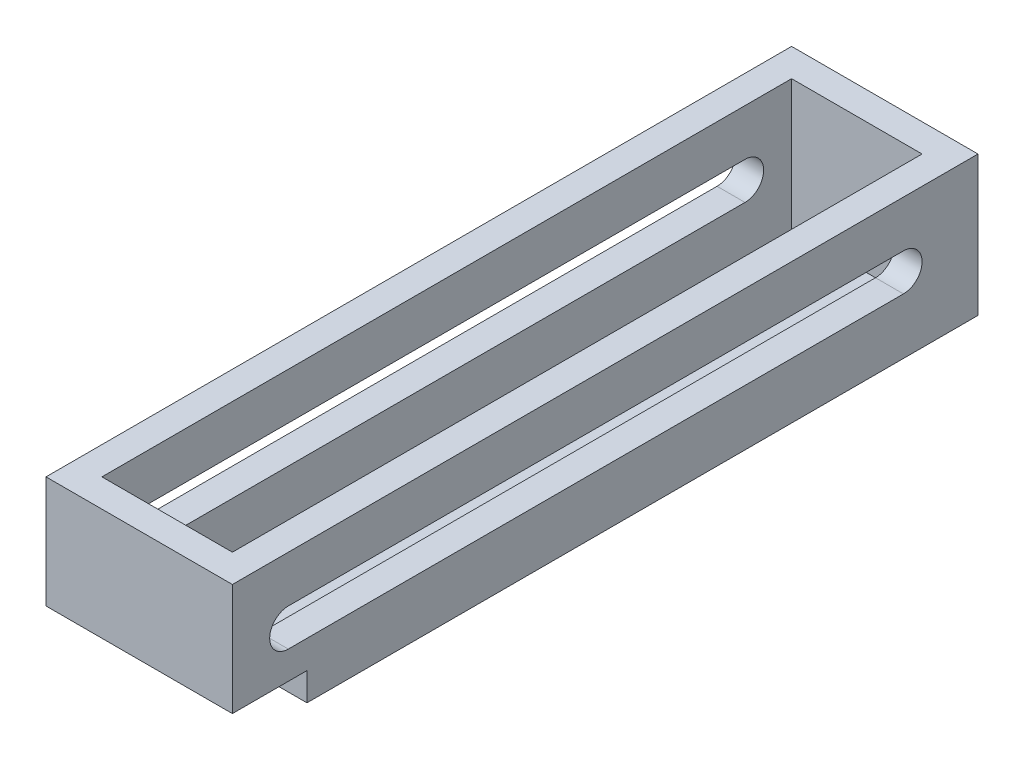
SolidWorks part; units mm, degrees
material "Oak"
ref_plane "Front Plane" through (0, 0, 0) normal (0, 0, 1) x (1, 0, 0)
ref_plane "Top Plane" through (0, 0, 0) normal (0, 1, 0) x (1, 0, 0)
ref_plane "Right Plane" through (0, 0, 0) normal (1, 0, 0) x (0, 0, -1)
other "Configuration Table"
sketch "Sketch1" plane through (0, 0, 0) normal (0, 1, 0) x (1, 0, 0)
  line L1 (-63.5, 254) -> (63.5, 254)
  line L2 (-63.5, 254) -> (-63.5, -254)
  line L3 (-63.5, -254) -> (63.5, -254)
  line L4 (63.5, 254) -> (63.5, -254)
  line L5 (-63.5, 254) -> (63.5, -254) construction
  line L6 (-63.5, -254) -> (63.5, 254) construction
  point P0 (0, 0)
  dimension "D1" = 508
  dimension "D2" = 127
extrude "Boss-Extrude1" add sketch "Sketch1" along normal blind 95.25
sketch "Sketch2" plane through (0, 95.25, 0) normal (0, 1, 0) x (1, 0, 0)
  line L0 (-44.45, 234.95) -> (44.45, 234.95)
  line L1 (44.45, 234.95) -> (44.45, -234.95)
  line L2 (44.45, -234.95) -> (-44.45, -234.95)
  line L3 (-44.45, -234.95) -> (-44.45, 234.95)
  line L4 (63.5, 254) -> (-63.5, 254) construction
  line L5 (-63.5, -254) -> (63.5, -254) construction
  line L6 (63.5, -254) -> (63.5, 254) construction
  line L7 (-63.5, 254) -> (-63.5, -254) construction
  dimension "D1" = 19.05
  dimension "D2" = 19.05
  dimension "D3" = 19.05
  dimension "D4" = 19.05
extrude "Cut-Extrude2" cut sketch "Sketch2" against normal blind 88.9
sketch "Sketch3" plane through (63.5, 0, 0) normal (1, 0, 0) x (0, 0, -1)
  line L1 (203.2, 50.8) -> (-215.9, 50.8) construction
  line L3 (203.2, 38.1) -> (-215.9, 38.1)
  line L4 (203.2, 63.5) -> (-215.9, 63.5)
  line L5 (-254, 0) -> (254, 0) construction
  line L6 (254, 95.25) -> (254, 0) construction
  arc A1 (203.2, 38.1) -> (203.2, 63.5) centre (203.2, 50.8) ccw
  arc A2 (-215.9, 63.5) -> (-215.9, 38.1) centre (-215.9, 50.8) ccw
  point P2 (-6.35, 50.8)
  dimension "D3" = 419.1
  dimension "D4" = 12.7
  dimension "D1" = 50.8
  dimension "D2" = 50.8
extrude "Cut-Extrude3" cut sketch "Sketch3" against normal through all
sketch "Sketch4" plane through (0, 0, 254) normal (0, 0, 1) x (1, 0, 0)
  line L0 (-63.5, 19.05) -> (63.5, 19.05)
  line L1 (-63.5, 95.25) -> (-63.5, 0) construction
  line L2 (63.5, 95.25) -> (63.5, 0) construction
  line L3 (63.5, 19.05) -> (63.5, 0)
  line L4 (63.5, 0) -> (-63.5, 0)
  line L5 (-63.5, 0) -> (-63.5, 19.05)
  line L6 (-63.5, 95.25) -> (63.5, 95.25) construction
  dimension "D1" = 76.2
extrude "Cut-Extrude4" cut sketch "Sketch4" against normal blind 50.8
